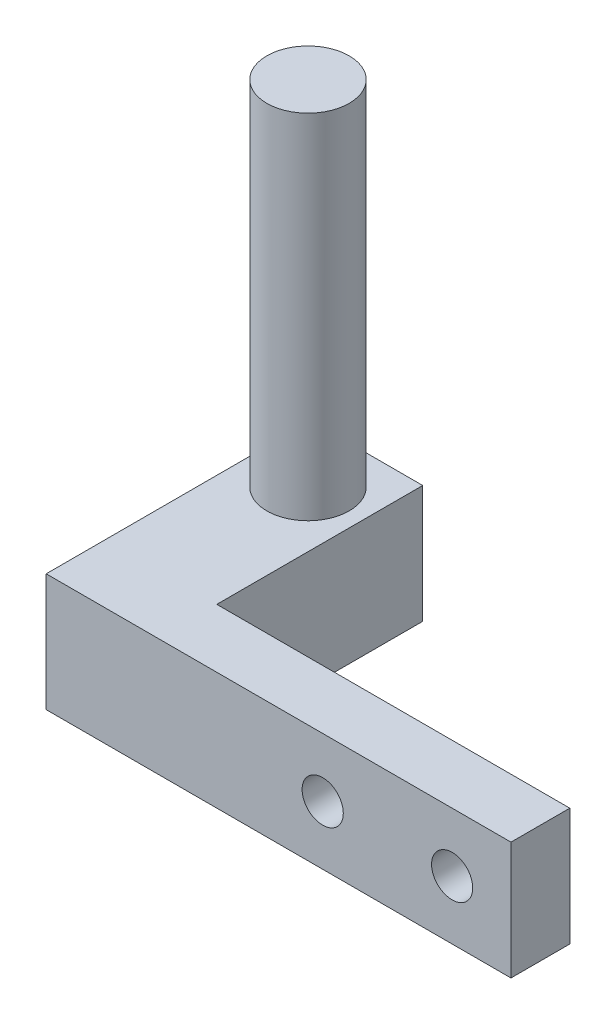
SolidWorks part; units mm, degrees
ref_plane "Front Plane" through (0, 0, 0) normal (0, 0, 1) x (1, 0, 0)
ref_plane "Top Plane" through (0, 0, 0) normal (0, 1, 0) x (1, 0, 0)
ref_plane "Right Plane" through (0, 0, 0) normal (1, 0, 0) x (0, 0, -1)
sketch "Sketch1" plane through (0, 0, 0) normal (0, 0, 1) x (1, 0, 0)
  line L1 (0, 0) -> (12.5, 0)
  line L2 (0, 0) -> (0, 10)
  line L3 (0, 10) -> (12.5, 10)
  line L4 (12.5, 0) -> (12.5, 10)
  dimension "D1" = 12.5
  dimension "D2" = 10
extrude "Boss-Extrude1" add sketch "Sketch1" along normal blind 10
sketch "Sketch2" plane through (0, 0, 0) normal (-1, 0, 0) x (0, 0, 1)
  line L0 (10, 0) -> (0, 0) construction
  line L1 (10, 0) -> (0, 0)
  line L2 (10, 0) -> (10, 10)
  line L3 (10, 10) -> (0, 10)
  line L4 (0, 0) -> (0, 10)
  line L5 (0, 10) -> (0, 0) construction
extrude "Boss-Extrude2" add sketch "Sketch2" along normal blind 5
sketch "Sketch3" plane through (0, 10, 0) normal (0, 1, 0) x (1, 0, 0)
  line L0 (12.5, -10) -> (12.5, 0) construction
  line L1 (12.5, 0) -> (-5, 0) construction
  circle A0 centre (3.75, -5) radius 3.5
  point P5 (12.5, -5)
  point P9 (3.75, 0)
  dimension "D1" = 7
extrude "Boss-Extrude3" add sketch "Sketch3" along normal blind 30
sketch "Sketch4" plane through (0, 10, 0) normal (0, 1, 0) x (1, 0, 0)
  line L0 (12.5, 0) -> (-5, 0) construction
  line L1 (12.5, 0) -> (8.5, 0)
  line L2 (12.5, 0) -> (12.5, -10)
  line L3 (12.5, -10) -> (8.5, -10)
  line L4 (8.5, 0) -> (8.5, -10)
  line L5 (12.5, -10) -> (-5, -10) construction
  line L6 (12.5, -10) -> (12.5, 0) construction
  line L7 (3.75, 0) -> (3.75, -3.716) construction
  line L8 (-5, -10) -> (-1, -10)
  line L9 (-5, 0) -> (-5, -10)
  line L10 (-5, 0) -> (-1, 0)
  line L11 (-1, 0) -> (-1, -10)
  dimension "D1" = 4
extrude "Cut-Extrude1" cut sketch "Sketch4" against normal through all
sketch "Sketch5" plane through (0, 0, 10) normal (0, 0, 1) x (1, 0, 0)
  line L0 (-1, 0) -> (8.5, 0) construction
  line L1 (8.5, 0) -> (-1, 0)
  line L2 (8.5, 0) -> (8.5, 10)
  line L3 (8.5, 10) -> (-1, 10)
  line L4 (-1, 0) -> (-1, 10)
  line L5 (-1, 0) -> (-1, 10) construction
  line L6 (8.5, 10) -> (-1, 10) construction
  line L7 (8.5, 0) -> (8.5, 10) construction
extrude "Boss-Extrude4" add sketch "Sketch5" along normal blind 12.5
sketch "Sketch6" plane through (8.5, 0, 0) normal (1, 0, 0) x (0, 0, -1)
  line L0 (0, 10) -> (-22.5, 10) construction
  line L1 (-22.5, 0) -> (-17.5, 0)
  line L2 (-22.5, 0) -> (-22.5, 10)
  line L3 (-22.5, 10) -> (-17.5, 10)
  line L4 (-17.5, 0) -> (-17.5, 10)
  line L5 (-22.5, 0) -> (-22.5, 10) construction
  line L6 (0, 0) -> (-22.5, 0) construction
  dimension "D1" = 5
extrude "Boss-Extrude5" add sketch "Sketch6" along normal blind 30
sketch "Sketch7" plane through (0, 0, 22.5) normal (0, 0, 1) x (1, 0, 0)
  line L0 (38.5, 10) -> (38.5, 0) construction
  circle A0 centre (22.5, 5) radius 1.75
  circle A1 centre (33.5, 5) radius 1.75
  point P6 (38.5, 5)
  dimension "D1" = 3.5
  dimension "D2" = 3.5
  dimension "D3" = 5
  dimension "D4" = 11
extrude "Cut-Extrude2" cut sketch "Sketch7" against normal through all
